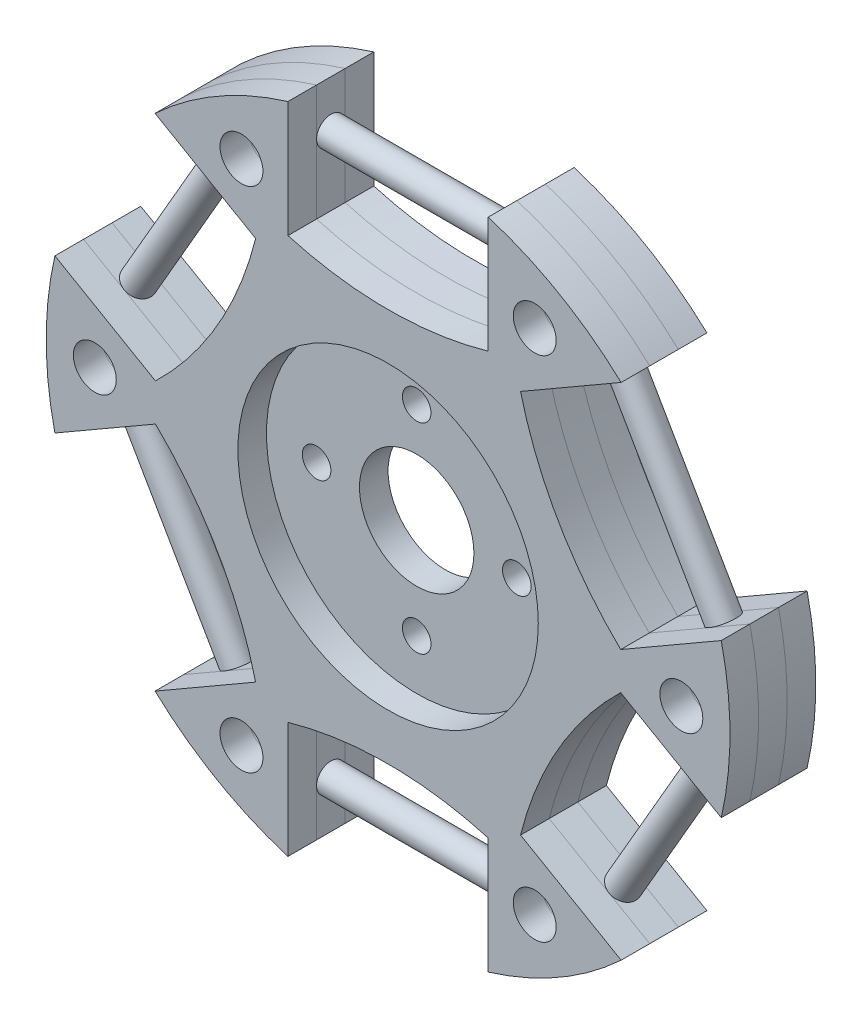
SolidWorks part; units mm, degrees
other "相机1"
material "1023 碳钢板 (SS)"
ref_plane "前视基准面" through (0, 0, 0) normal (0, 0, 1) x (1, 0, 0)
ref_plane "上视基准面" through (0, 0, 0) normal (0, 1, 0) x (1, 0, 0)
ref_plane "右视基准面" through (0, 0, 0) normal (1, 0, 0) x (0, 0, -1)
sketch "草图1" plane through (0, 0, 0) normal (0, 0, 1) x (1, 0, 0)
  circle A0 centre (0, 0) radius 25.4
  circle A1 centre (0, 0) radius 10.5
  dimension "D1" = 50.8
  dimension "D2" = 21
extrude "凸台-拉伸1" add sketch "草图1" along normal blind 2
sketch "草图2" plane through (0, 0, 2) normal (0, 0, 1) x (1, 0, 0)
  circle A0 centre (0, 0) radius 25.4
  circle A1 centre (0, 0) radius 4
  dimension "D1" = 8
extrude "凸台-拉伸2" add sketch "草图2" along normal blind 2 separate body
sketch "草图3" plane through (0, 0, 4) normal (0, 0, 1) x (1, 0, 0)
  circle A0 centre (0, 0) radius 25.4
  circle A1 centre (0, 0) radius 10.5
  dimension "D1" = 21
extrude "凸台-拉伸3" add sketch "草图3" along normal blind 2 separate body
sketch "草图4" plane through (0, 0, 6) normal (0, 0, 1) x (1, 0, 0)
  line L0 (9.2597, 13.429) -> (17.6452, 18.2704)
  line L1 (7, 14.7336) -> (7, 24.4164)
  line L2 (-7, 14.7336) -> (-7, 24.4164)
  line L3 (16.2597, 1.3046) -> (24.6452, 6.146)
  line L4 (16.2597, -1.3046) -> (24.6452, -6.146)
  line L5 (9.2597, -13.429) -> (17.6452, -18.2704)
  line L6 (7, -14.7336) -> (7, -24.4164)
  line L7 (-7, -14.7336) -> (-7, -24.4164)
  line L8 (-9.2597, -13.429) -> (-17.6452, -18.2704)
  line L9 (-16.2597, -1.3046) -> (-24.6452, -6.146)
  line L10 (-16.2597, 1.3046) -> (-24.6452, 6.146)
  line L11 (-9.2597, 13.429) -> (-17.6452, 18.2704)
  arc A0 (7, 24.4164) -> (-7, 24.4164) centre (0, 0) ccw
  arc A1 (9.2597, 13.429) -> (16.2597, 1.3046) centre (33.9049, 19.575) ccw
  arc A2 (-7, 14.7336) -> (7, 14.7336) centre (0, 39.15) ccw
  arc A3 (24.6452, 6.146) -> (17.6452, 18.2704) centre (0, 0) ccw
  arc A4 (16.2597, -1.3046) -> (9.2597, -13.429) centre (33.9049, -19.575) ccw
  arc A5 (17.6452, -18.2704) -> (24.6452, -6.146) centre (0, 0) ccw
  arc A6 (7, -14.7336) -> (-7, -14.7336) centre (0, -39.15) ccw
  arc A7 (-7, -24.4164) -> (7, -24.4164) centre (0, 0) ccw
  arc A8 (-9.2597, -13.429) -> (-16.2597, -1.3046) centre (-33.9049, -19.575) ccw
  arc A9 (-24.6452, -6.146) -> (-17.6452, -18.2704) centre (0, 0) ccw
  arc A10 (-16.2597, 1.3046) -> (-9.2597, 13.429) centre (-33.9049, 19.575) ccw
  arc A11 (-17.6452, 18.2704) -> (-24.6452, 6.146) centre (0, 0) ccw
  point P34 (0, 0)
  dimension "D1" = 50.8
  dimension "D2" = 6
  dimension "D3" = 50.8
extrude "切除-拉伸1" cut sketch "草图4" against normal blind 20.5
sketch "草图5" plane through (0, 0, 6) normal (0, 0, 1) x (1, 0, 0)
  circle A0 centre (0, 0) radius 4 construction
  circle A2 centre (10.25, 17.7535) radius 1.5
  circle A3 centre (20.5, 0) radius 1.5
  circle A4 centre (10.25, -17.7535) radius 1.5
  circle A5 centre (-10.25, -17.7535) radius 1.5
  circle A6 centre (-20.5, 0) radius 1.5
  circle A7 centre (-10.25, 17.7535) radius 1.5
  point P21 (0, 0)
  dimension "D1" = 20.5
  dimension "D2" = 3
  dimension "D3" = 6
extrude "切除-拉伸2" cut sketch "草图5" against normal blind 20.5
sketch "草图6" plane through (-7, 0, 0) normal (1, 0, 0) x (0, 0, -1)
  line L0 (-2, 24.4164) -> (-2, 14.7336) construction
  circle A0 centre (-3, 19.575) radius 1
  dimension "D1" = 2
  dimension "D2" = 1
extrude "凸台-拉伸4" add sketch "草图6" along normal blind 14
pattern_circular "阵列(圆周)1" count 6 over 360 about axis through (0, 0, 6) along (0, 0, 1) of "凸台-拉伸4"
sketch "草图7" plane through (0, 0, 4) normal (0, 0, 1) x (1, 0, 0)
  circle A1 centre (0, 7) radius 1
  circle A2 centre (7, 0) radius 1
  circle A3 centre (0, -7) radius 1
  circle A4 centre (-7, 0) radius 1
  point P14 (0, 0)
  dimension "D2" = 2
  dimension "D3" = 4
extrude "切除-拉伸3" cut sketch "草图7" against normal blind 14
sketch "草图8" plane through (0, 0, 6) normal (0, 0, 1) x (1, 0, 0)
  circle A0 centre (0, 0) radius 23.9
  dimension "D1" = 47.8
extrude "切除-拉伸-薄壁1" cut sketch "草图8" against normal blind 10 thin
